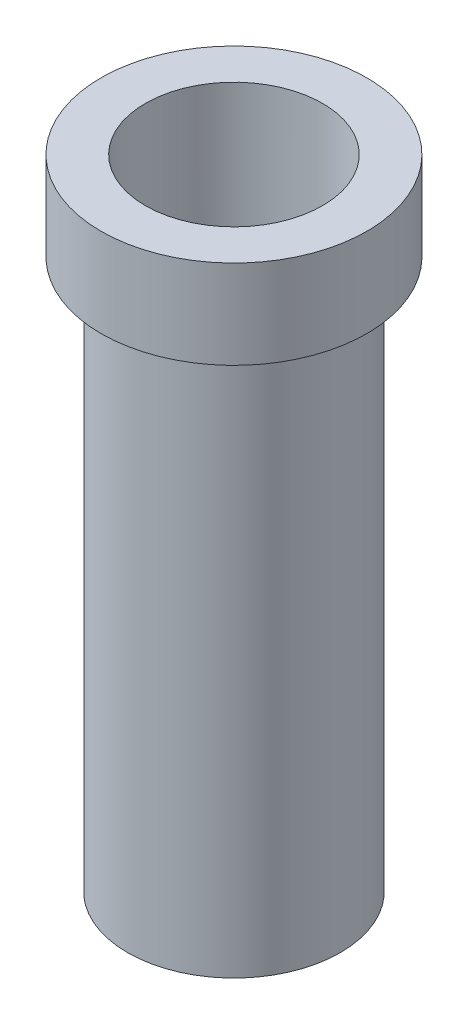
SolidWorks part; units mm, degrees
ref_plane "Face" through (0, 0, 0) normal (0, 0, 1) x (1, 0, 0)
ref_plane "Dessus" through (0, 0, 0) normal (0, 1, 0) x (1, 0, 0)
ref_plane "Droite" through (0, 0, 0) normal (1, 0, 0) x (0, 0, -1)
sketch "Esquisse1" plane through (0, 0, 0) normal (0, 1, 0) x (1, 0, 0)
  circle A0 centre (0, 0) radius 7.5
  dimension "D1" = 15
extrude "Extrusion1" add sketch "Esquisse1" along normal blind 5
sketch "Esquisse2" plane through (0, 0, 0) normal (0, -1, 0) x (1, 0, 0)
  circle A0 centre (0, 0) radius 6
  dimension "D1" = 12
extrude "Extrusion2" add sketch "Esquisse2" along normal blind 31
sketch "Esquisse3" plane through (0, 5, 0) normal (0, 1, 0) x (1, 0, 0)
  circle A0 centre (0, 0) radius 5
  dimension "D1" = 10
extrude "Extrusion3" cut sketch "Esquisse3" against normal up to next
